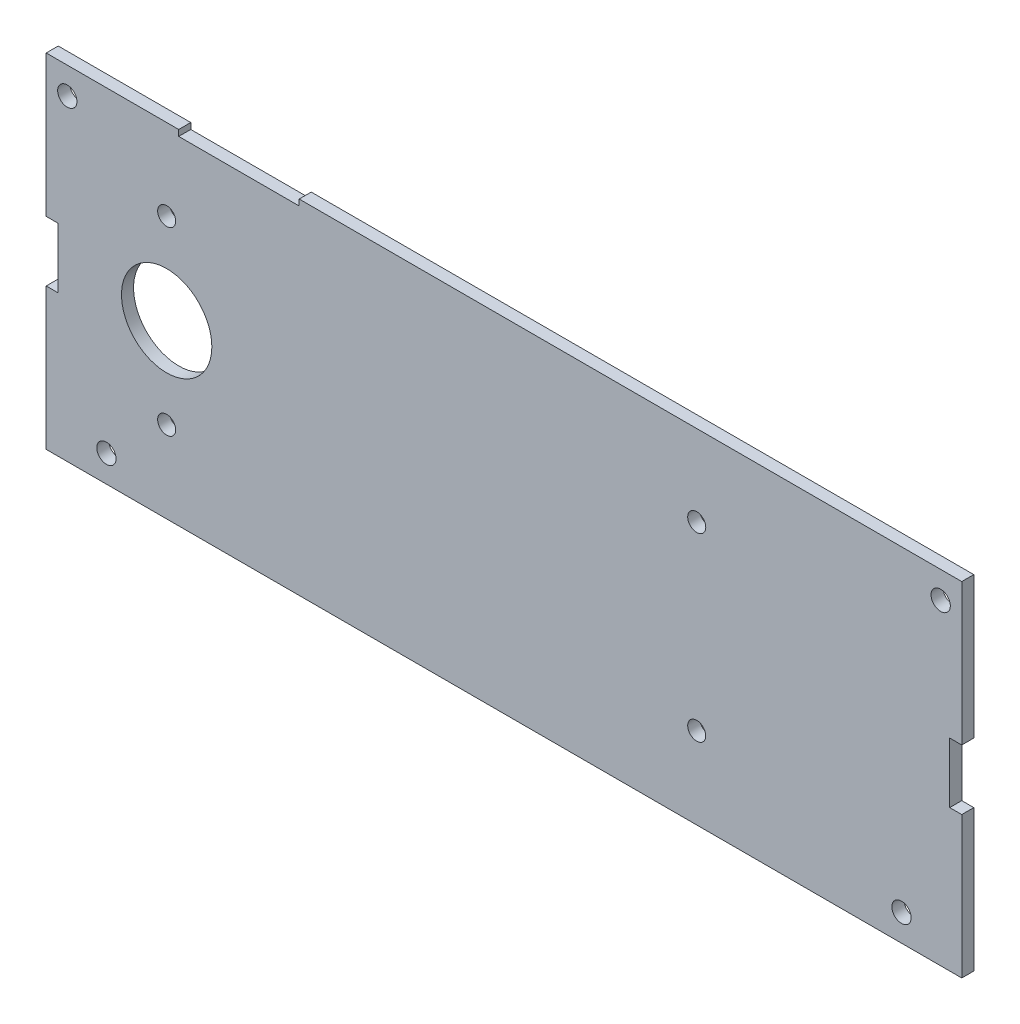
SolidWorks part; units mm, degrees
ref_plane "Front Plane" through (0, 0, 0) normal (0, 0, 1) x (1, 0, 0)
ref_plane "Top Plane" through (0, 0, 0) normal (0, 1, 0) x (1, 0, 0)
ref_plane "Right Plane" through (0, 0, 0) normal (1, 0, 0) x (0, 0, -1)
sketch "Sketch1" plane through (0, 0, 0) normal (0, 0, 1) x (1, 0, 0)
  line L0 (0, 11.7491) -> (0, -12.7107) construction
  line L1 (-76, 28.5) -> (76, 28.5)
  line L2 (-76, 28.5) -> (-76, -28.5)
  line L3 (-76, -28.5) -> (76, -28.5)
  line L4 (76, 28.5) -> (76, -28.5)
  line L5 (-76, 28.5) -> (76, -28.5) construction
  line L6 (-76, -28.5) -> (76, 28.5) construction
  line L7 (-74, 5) -> (-78, 5)
  line L8 (-74, 5) -> (-74, -5)
  line L9 (-74, -5) -> (-78, -5)
  line L10 (-78, 5) -> (-78, -5)
  line L11 (-74, 5) -> (-78, -5) construction
  line L12 (-74, -5) -> (-78, 5) construction
  line L13 (74, -5) -> (78, 5) construction
  line L14 (74, 5) -> (78, -5) construction
  line L15 (78, 5) -> (78, -5)
  line L16 (74, -5) -> (78, -5)
  line L17 (74, 5) -> (74, -5)
  line L18 (74, 5) -> (78, 5)
  point P0 (0, 0)
  point P6 (-76, 0)
  point P17 (76, 0)
  dimension "D1" = 57
  dimension "D2" = 152
  dimension "D3" = 10
  dimension "D4" = 4
extrude "Boss-Extrude1" add sketch "Sketch1" along normal blind 2 contours L17 L18 L4 L1 L2 L7 L8 L9 L3 L16
sketch "Sketch2" plane through (0, 0, 2) normal (0, 0, 1) x (1, 0, 0)
  line L1 (-76, -5) -> (-76, -28.5) construction
  circle A0 centre (-72.5, 24.05) radius 1.6
  circle A1 centre (72.5, 24.05) radius 1.6
  circle A2 centre (66, -24.05) radius 1.6
  circle A3 centre (-66, -24.05) radius 1.6
  circle A4 centre (-56, 0) radius 7.5
  dimension "D1" = 3.2
  dimension "D2" = 3.2
  dimension "D3" = 3.2
  dimension "D4" = 3.2
  dimension "D5" = 15
  dimension "D9" = 66
  dimension "D12" = 24.05
  dimension "D14" = 24.05
  dimension "D6" = 0
  dimension "D7" = 72.5
  dimension "D8" = 72.5
  dimension "D10" = 66
  dimension "D11" = 24.05
  dimension "D13" = 24.05
  dimension "D15" = 20
extrude "Cut-Extrude1" cut sketch "Sketch2" against normal through all
sketch "Sketch3" plane through (0, 0, 2) normal (0, 0, 1) x (1, 0, 0)
  line L0 (-76, -5) -> (-76, -28.5) construction
  line L1 (-46.668, 0.05) -> (-25.3244, 0.05) construction
  line L2 (-12, -12.6127) -> (-12, -0.6118) construction
  line L3 (-76, -28.5) -> (76, -28.5) construction
  line L4 (-76, 28.5) -> (76, 28.5) construction
  line L5 (-54, 28.5) -> (-34, 28.5)
  line L6 (-54, 28.5) -> (-54, 27.5)
  line L7 (-54, 27.5) -> (-34, 27.5)
  line L8 (-34, 28.5) -> (-34, 27.5)
  line L9 (-76, 28.5) -> (-76, 5) construction
  circle A0 centre (-56, -14.95) radius 1.5
  circle A1 centre (-56, 15.05) radius 1.5
  circle A2 centre (-56, -14.95) radius 1.5
  circle A3 centre (-56, 15.05) radius 1.5
  circle A4 centre (32, 15.05) radius 1.5
  circle A5 centre (32, -14.95) radius 1.5
  dimension "D1" = 3
  dimension "D2" = 20
  dimension "D3" = 15
  dimension "D4" = 44
  dimension "D5" = 13.55
  dimension "D6" = 1
  dimension "D7" = 20
  dimension "D8" = 22
extrude "Cut-Extrude2" cut sketch "Sketch3" against normal through all both and the other way through all contours A5 | A1 | A0 | A4 | L6 L5 L8 L7
